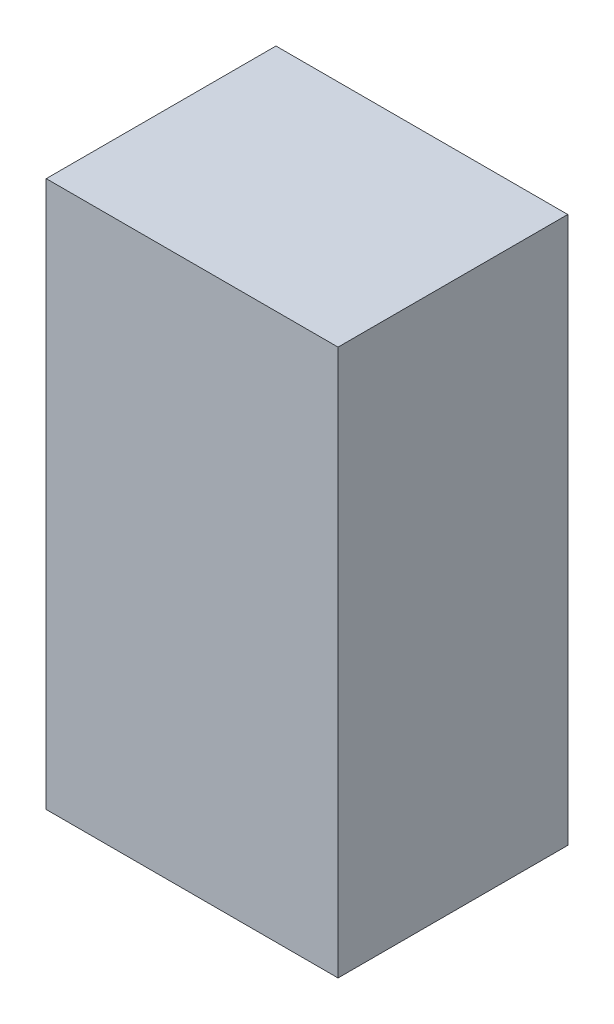
SolidWorks part; units mm, degrees
ref_plane "Front Plane" through (0, 0, 0) normal (0, 0, 1) x (1, 0, 0)
ref_plane "Top Plane" through (0, 0, 0) normal (0, 1, 0) x (1, 0, 0)
ref_plane "Right Plane" through (0, 0, 0) normal (1, 0, 0) x (0, 0, -1)
sketch "Sketch1" plane through (0, 0, 0) normal (0, 1, 0) x (1, 0, 0)
  line L1 (-298.45, -234.95) -> (298.45, -234.95)
  line L2 (-298.45, -234.95) -> (-298.45, 234.95)
  line L3 (-298.45, 234.95) -> (298.45, 234.95)
  line L4 (298.45, -234.95) -> (298.45, 234.95)
  line L5 (-298.45, -234.95) -> (298.45, 234.95) construction
  line L6 (-298.45, 234.95) -> (298.45, -234.95) construction
  point P0 (0, 0)
  dimension "D1" = 596.9
  dimension "D2" = 469.9
extrude "Boss-Extrude1" add sketch "Sketch1" along normal blind 1117.6
